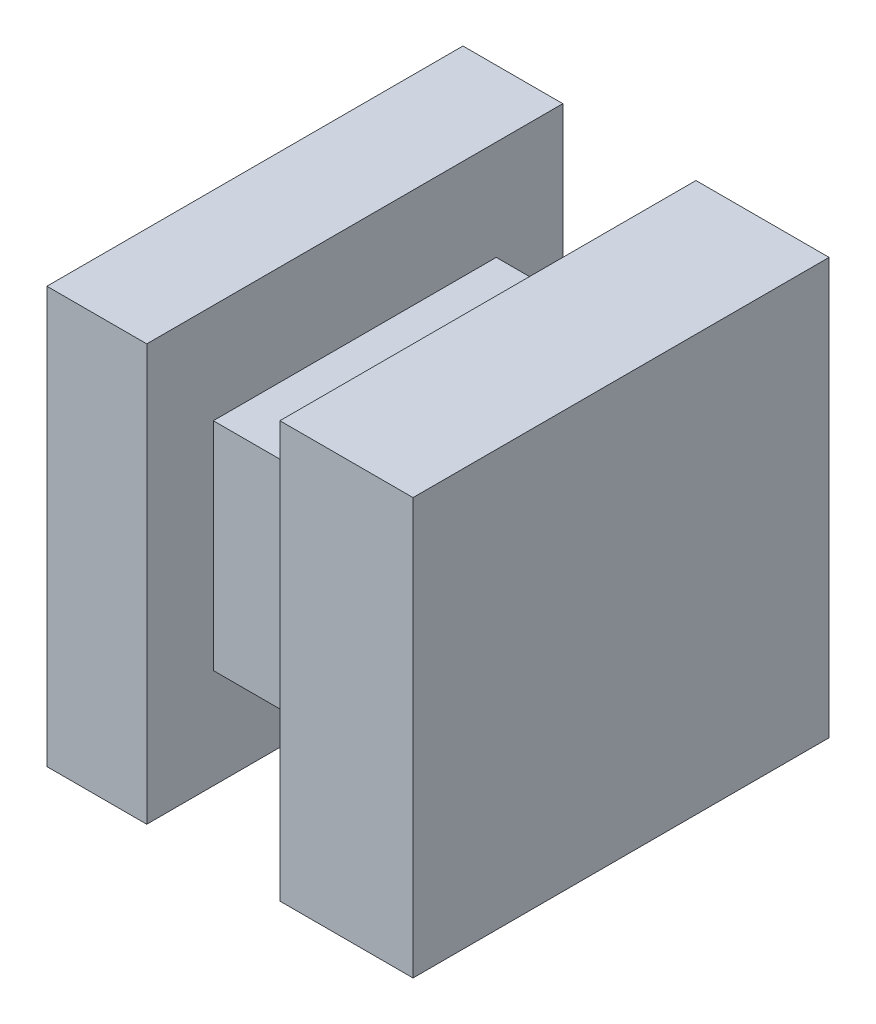
SolidWorks part; units mm, degrees
ref_plane "Front Plane" through (0, 0, 0) normal (0, 0, 1) x (1, 0, 0)
ref_plane "Top Plane" through (0, 0, 0) normal (0, 1, 0) x (1, 0, 0)
ref_plane "Right Plane" through (0, 0, 0) normal (1, 0, 0) x (0, 0, -1)
sketch "Sketch1" plane through (0, 0, 0) normal (0, 0, 1) x (1, 0, 0)
  line L0 (-90.6146, 45.4594) -> (-87.6146, 45.4594)
  line L1 (-87.6146, 45.4594) -> (-87.6146, 42.4594)
  line L2 (-90.6146, 45.4594) -> (-90.6146, 32.9594)
  line L3 (-90.6146, 32.9594) -> (-87.6146, 32.9594)
  line L4 (-87.6146, 32.9594) -> (-87.6146, 35.9594)
  line L5 (-87.6146, 35.9594) -> (-83.6146, 35.9594)
  line L6 (-83.6146, 35.9594) -> (-83.6146, 32.9594)
  line L7 (-83.6146, 32.9594) -> (-79.6146, 32.9594)
  line L8 (-87.6146, 42.4594) -> (-83.6146, 42.4594)
  line L9 (-83.6146, 42.4594) -> (-83.6146, 45.4594)
  line L10 (-83.6146, 45.4594) -> (-79.6146, 45.4594)
  line L12 (-79.6146, 45.4594) -> (-79.6146, 32.9594)
extrude "Boss-Extrude2" add sketch "Sketch1" along normal blind 12.5
sketch "Sketch7" plane through (0, 42.4594, 0) normal (0, 1, 0) x (1, 0, 0)
  line L0 (-87.6146, -12.5) -> (-87.6146, -10.5) construction
  line L1 (-87.6146, -12.5) -> (-87.6146, 0) construction
  line L2 (-87.6146, -10.5) -> (-83.6146, -10.5)
  line L3 (-83.6146, -12.5) -> (-83.6146, 0) construction
  line L4 (-83.6146, -10.5) -> (-83.6146, -12.5)
  line L9 (-83.6146, 0) -> (-87.6146, 0)
  line L10 (-87.6146, 0) -> (-87.6146, -12.5)
  line L11 (-87.6146, -12.5) -> (-83.6146, -12.5)
  line L12 (-83.6146, -12.5) -> (-83.6146, 0)
  line L14 (-87.6146, -10.5) -> (-87.6146, -12.5)
  line L15 (-87.6146, -12.5) -> (-83.6146, -12.5)
  dimension "D1" = 0
extrude "Cut-Extrude10" cut sketch "Sketch7" against normal blind 26
sketch "Sketch8" plane through (0, 42.4594, 0) normal (0, 1, 0) x (1, 0, 0)
  line L0 (-87.6146, 0) -> (-87.6146, -2)
  line L1 (-87.6146, -10.5) -> (-87.6146, 0) construction
  line L2 (-87.6146, -2) -> (-83.6146, -2)
  line L3 (-83.6146, -10.5) -> (-83.6146, 0) construction
  line L4 (-83.6146, -2) -> (-83.6146, 0)
extrude "Cut-Extrude11" cut sketch "Sketch8" against normal through all and the other way through all
